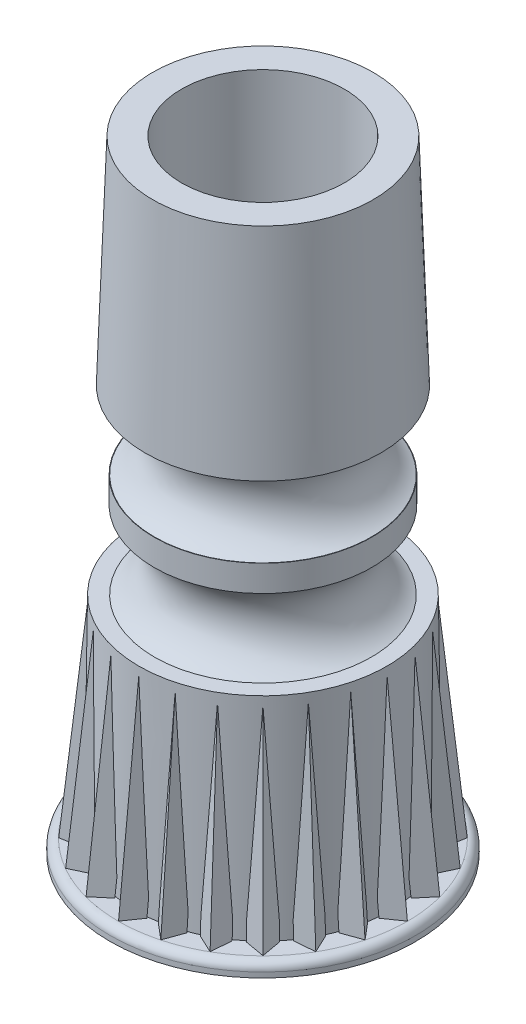
SolidWorks part; units mm, degrees
material "CA"
ref_plane "Front Plane" through (0, 0, 0) normal (0, 0, 1) x (1, 0, 0)
ref_plane "Top Plane" through (0, 0, 0) normal (0, 1, 0) x (1, 0, 0)
ref_plane "Right Plane" through (0, 0, 0) normal (1, 0, 0) x (0, 0, -1)
sketch "Sketch1" plane through (0, 0, 0) normal (0, 1, 0) x (1, 0, 0)
  circle A0 centre (0, 0) radius 9.3345
  dimension "D1" = 18.669
extrude "Boss-Extrude1" add sketch "Sketch1" along normal blind 0.8128 draft 1
ref_plane "Plane1" through (0, 13.6652, 0) normal (0, 1, 0) x (1, 0, 0)
sketch "Sketch2" plane through (0, 13.6652, 0) normal (0, 1, 0) x (1, 0, 0)
  circle A0 centre (0, 0) radius 7.5692
  dimension "D1" = 15.1384
sketch "Sketch3" plane through (0, 0.8128, 0) normal (0, 1, 0) x (1, 0, 0)
  circle A0 centre (0, 0) radius 7.7343
  dimension "D1" = 15.4686
loft "Loft1" add profiles "Sketch2", "Sketch3"
sketch "Sketch4" plane through (0, 0, 0) normal (1, 0, 0) x (0, 0, -1)
  line L0 (-7.5692, 13.6652) -> (-7.7343, 0.8128) construction
  line L1 (-7.5757, 13.1572) -> (-7.7343, 0.8128) construction
  line L2 (-9.3203, 0.8128) -> (-9.3345, 0) construction
  line L3 (-9.3203, 0.8128) -> (-9.3345, 0) construction
  line L4 (-9.3203, 0.8128) -> (-7.5757, 13.1572) construction
  line L5 (-9.3203, 0.8128) -> (-8.8123, 0.8128) construction
  line L6 (7.5692, 13.6652) -> (-7.5692, 13.6652) construction
  line L7 (-8.8123, 0.8128) -> (-7.5757, 13.1572)
  dimension "D1" = 0.508
  dimension "D2" = 0.508
ref_plane "Plane2" through (0, 0.8128, 8.8123) normal (0, 0.995, -0.0997) x (1, 0, 0)
sketch "Sketch14" plane through (0, 0.8128, 8.8123) normal (0, 0.995, -0.0997) x (1, 0, 0)
  line L0 (0, 0) -> (-0.7114, 1.016)
  line L1 (0, 0) -> (0, 1.1937) construction
  line L2 (0, 0) -> (0.7114, 1.016)
  line L3 (-0.7114, 1.016) -> (0.7114, 1.016)
  dimension "D1" = 1.016
  dimension "D2" = 70
sweep "Sweep1" add profiles "Sketch14" path "Sketch4"
sketch "Sketch7" plane through (0, 0, 0) normal (1, 0, 0) x (0, 0, -1)
  line L0 (0, 0) -> (0, 29.555) construction
  line L1 (0, 0.8128) -> (0, 13.6652) construction
  line L2 (6.6421, 19.2151) -> (8.5101, 19.2151) construction
  line L3 (6.6421, 18.415) -> (6.6167, 18.415)
  line L4 (7.5692, 13.6652) -> (-7.5692, 13.6652) construction
  line L5 (6.6421, 20.0152) -> (6.6421, 18.415)
  line L6 (16.7407, 13.6652) -> (0, 13.6652) construction
  line L7 (6.6167, 13.6652) -> (0, 13.6652)
  line L8 (0, 13.6652) -> (0, 26.2128)
  line L9 (6.6421, 20.0152) -> (6.6167, 20.0152)
  line L10 (6.6167, 24.765) -> (6.6167, 26.2128)
  line L11 (6.6167, 26.2128) -> (0, 26.2128)
  arc A0 (6.6167, 20.0152) -> (6.6167, 24.765) centre (7.7051, 22.3901) cw
  arc A1 (6.6167, 18.415) -> (6.6167, 13.6652) centre (7.7051, 16.0401) ccw
  dimension "D4" = 10.1854
  dimension "D1" = 13.2334
  dimension "D2" = 0.0254
  dimension "D3" = 1.4478
  dimension "D5" = 4.7498
  dimension "D6" = 4.7498
  dimension "D7" = 1.6002
pattern_circular "CirPattern3" count 24 over 360 about axis through (0, 0, 0) along (0, 1, 0) of "Sweep1"
revolve "Revolve1" add sketch "Sketch7" angle 360 about L8
sketch "Sketch19" plane through (0, 0, 0) normal (1, 0, 0) x (0, 0, -1)
  line L0 (3.2004, 0) -> (3.4123, 12.1412)
  line L1 (0, 0) -> (0, 13.0728) construction
  line L2 (0, 0.8128) -> (0, 13.6652) construction
  line L3 (7.0644, 13.6652) -> (2.6809, 13.6652) construction
  line L4 (7.5692, 13.6652) -> (-7.5692, 13.6652) construction
  line L5 (3.4123, 12.1412) -> (5.5672, 12.1412)
  line L6 (3.2004, 0) -> (3.2004, -2.54)
  line L7 (3.2004, -2.54) -> (6.6294, -2.54)
  line L8 (5.5672, 12.1412) -> (6.6294, 0)
  line L9 (6.6294, 0) -> (6.6294, -2.54)
  circle A0 centre (0, 0) radius 3.2004 construction
  dimension "D1" = 6.4008
  dimension "D2" = 1
  dimension "D3" = 1.524
  dimension "D4" = 2.54
  dimension "D5" = 5
  dimension "D6" = 3.429
revolve "Cut-Revolve1" cut sketch "Sketch19" angle 360 about L1
fillet "Fillet1" radius 0.508 1 edges at (0, 0.8128, 9.3203)
ref_plane "Plane3" through (0, 37.8968, 0) normal (0, -1, 0) x (-1, 0, 0)
sketch "Sketch20" plane through (0, 37.8968, 0) normal (0, -1, 0) x (-1, 0, 0)
  circle A0 centre (0, 0) radius 6.731
  dimension "D1" = 13.462
extrude "Boss-Extrude2" add sketch "Sketch20" along normal blind 13.1572 draft 2 draft outward yes
sketch "Sketch21" plane through (0, 37.8968, 0) normal (0, 1, 0) x (1, 0, 0)
  circle A0 centre (0, 0) radius 4.9657
  dimension "D1" = 9.9314
extrude "Cut-Extrude1" cut sketch "Sketch21" against normal blind 12.2174
sketch "Sketch22" plane through (0, 0, 0) normal (0, -1, 0) x (1, 0, 0)
  circle A0 centre (0, 0) radius 2.1971
  dimension "D1" = 4.3942
extrude "Cut-Extrude2" cut sketch "Sketch22" against normal through all
